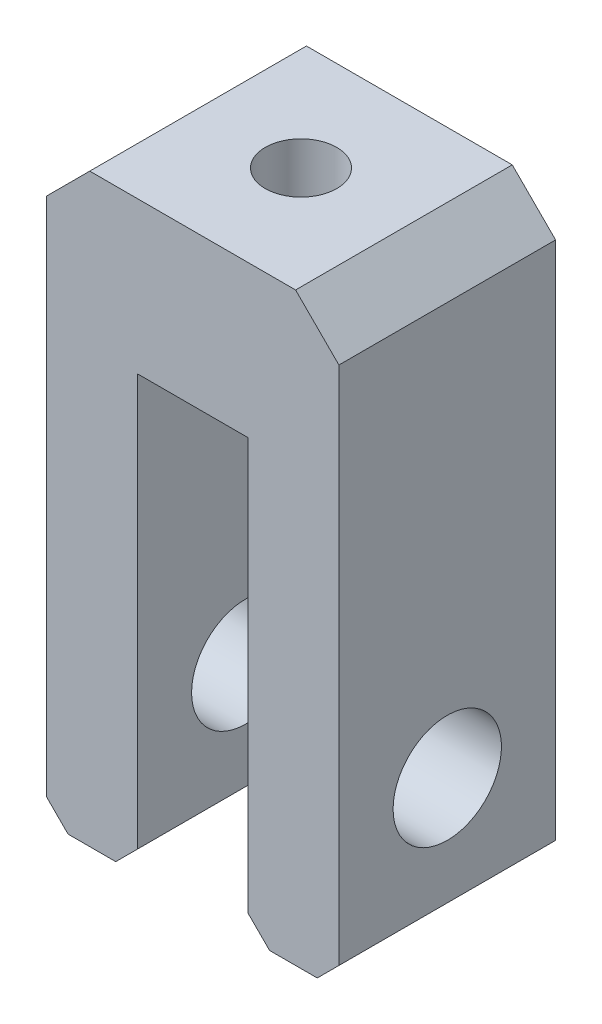
SolidWorks part; units mm, degrees
material "6061 合金"
ref_plane "前视基准面" through (0, 0, 0) normal (0, 0, 1) x (1, 0, 0)
ref_plane "上视基准面" through (0, 0, 0) normal (0, 1, 0) x (1, 0, 0)
ref_plane "右视基准面" through (0, 0, 0) normal (1, 0, 0) x (0, 0, -1)
sketch "草图1" plane through (0, 0, 0) normal (0, 0, 1) x (1, 0, 0)
  line L0 (0, 0) -> (0, 18.0058) construction
  line L1 (0, 0) -> (6.75, 0) construction
  line L2 (6.75, 0) -> (6.75, 27)
  line L3 (6.75, 27) -> (-6.75, 27)
  line L4 (6.75, 0) -> (2.55, 0)
  line L5 (2.55, 0) -> (2.55, 20)
  line L6 (2.55, 20) -> (-2.55, 20)
  line L7 (-6.75, 0) -> (-2.55, 0)
  line L8 (-2.55, 0) -> (-2.55, 20)
  line L9 (-6.75, 0) -> (-6.75, 27)
  point P6 (0, 20)
  point P13 (0, 27)
  dimension "D1" = 4.2
  dimension "D2" = 5.1
  dimension "D3" = 20
  dimension "D4" = 27
extrude "凸台-拉伸1" add sketch "草图1" along normal blind 10
sketch "草图2" plane through (-6.75, 0, 0) normal (-1, 0, 0) x (0, 0, 1)
  line L0 (5, 0) -> (5, 6) construction
  line L1 (10, 0) -> (0, 0) construction
  circle A0 centre (5, 6) radius 2.5
  dimension "D2" = 5
  dimension "D1" = 6
extrude "切除-拉伸1" cut sketch "草图2" against normal up to surface (13.5 mm away) up to face at (6.75, 13.5, 5)
sketch "草图3" plane through (0, 20, 0) normal (0, -1, 0) x (1, 0, 0)
  line L0 (0, 0) -> (0, 10) construction
  line L1 (-2.55, 0) -> (2.55, 0) construction
  line L2 (-2.55, 10) -> (2.55, 10) construction
  circle A0 centre (0, 5) radius 2.1
  dimension "D1" = 4.2
extrude "切除-拉伸2" [suppressed] cut sketch "草图3" against normal up to next
sketch "草图4" plane through (0, 0, 0) normal (0, 0, -1) x (-1, 0, 0)
  line L0 (-2.55, 20) -> (-2.55, 0) construction
  line L1 (2.55, 0) -> (2.55, 20) construction
  circle A0 centre (-2.55, 18.495) radius 1.505
  circle A1 centre (2.55, 18.495) radius 1.505
  dimension "D1" = 3.01
  dimension "D2" = 3.01
extrude "切除-拉伸3" [suppressed] cut sketch "草图4" against normal up to next
sketch "草图5" plane through (0, 0, 0) normal (0, 0, -1) x (-1, 0, 0)
  line L1 (-6.75, 0) -> (-6.75, 27) construction
  line L3 (-6.25, 3.5) -> (-7.25, 3.5)
  line L4 (-6.25, 3.5) -> (-6.25, 8.5)
  line L5 (-6.25, 8.5) -> (-7.25, 8.5)
  line L6 (-7.25, 3.5) -> (-7.25, 8.5)
  line L7 (-6.25, 3.5) -> (-7.25, 8.5) construction
  line L8 (-6.25, 8.5) -> (-7.25, 3.5) construction
  line L9 (-6.75, 27) -> (6.75, 27) construction
  line L10 (-2.1, 26.5) -> (2.1, 26.5)
  line L11 (-2.1, 26.5) -> (-2.1, 27.5)
  line L12 (-2.1, 27.5) -> (2.1, 27.5)
  line L13 (2.1, 26.5) -> (2.1, 27.5)
  line L14 (-2.1, 26.5) -> (2.1, 27.5) construction
  line L15 (-2.1, 27.5) -> (2.1, 26.5) construction
  line L16 (-2.55, 0) -> (-6.75, 0) construction
  line L17 (0, 12.8499) -> (0, -3.4001) construction
  line L18 (6.25, 8.5) -> (7.25, 3.5) construction
  line L19 (6.25, 3.5) -> (7.25, 8.5) construction
  line L20 (7.25, 3.5) -> (7.25, 8.5)
  line L21 (6.25, 8.5) -> (7.25, 8.5)
  line L22 (6.25, 3.5) -> (6.25, 8.5)
  line L23 (6.25, 3.5) -> (7.25, 3.5)
  point P0 (-6.75, 6)
  point P8 (0, 27)
  point P25 (6.75, 6)
  dimension "D1" = 5
  dimension "D3" = 6
  dimension "D2" = 1
  dimension "D4" = 4.2
  dimension "D5" = 1
hole_wizard "M4 螺纹孔1" positions "草图7" profile "草图6" tap size "M4" standard "GB" end condition through all
sketch "草图7" plane through (0, 27, 0) normal (0, 1, 0) x (1, 0, 0)
  line L0 (-6.75, -10) -> (-6.75, 0) construction
  point P0 (0, -5)
  point P4 (-6.75, -5)
sketch "草图6" plane through (0, 27, 5) normal (1, 0, 0) x (0, 0, 1)
  line L0 (0, 0) -> (0, 27)
  line L1 (0, 27) -> (1.65, 27)
  line L2 (1.65, 27) -> (1.65, 0)
  line L5 (1.65, 0) -> (0, 0)
  line L11 (0, -6.35) -> (0, 107.95) construction
  dimension "通孔螺纹孔钻头直径" = 3.3
  dimension "通孔螺纹孔钻头深度" = 27
cosmetic thread "孔螺蚊线1" parameters "D2"=4
chamfer "倒角1" distance 1 angle 45 4 edges at (6.75, 0, 5) (2.55, 0, 5) (-2.55, 0, 5) (-6.75, 0, 5)
chamfer "倒角2" distance 2 angle 45 2 edges at (6.75, 27, 5) (-6.75, 27, 5)
